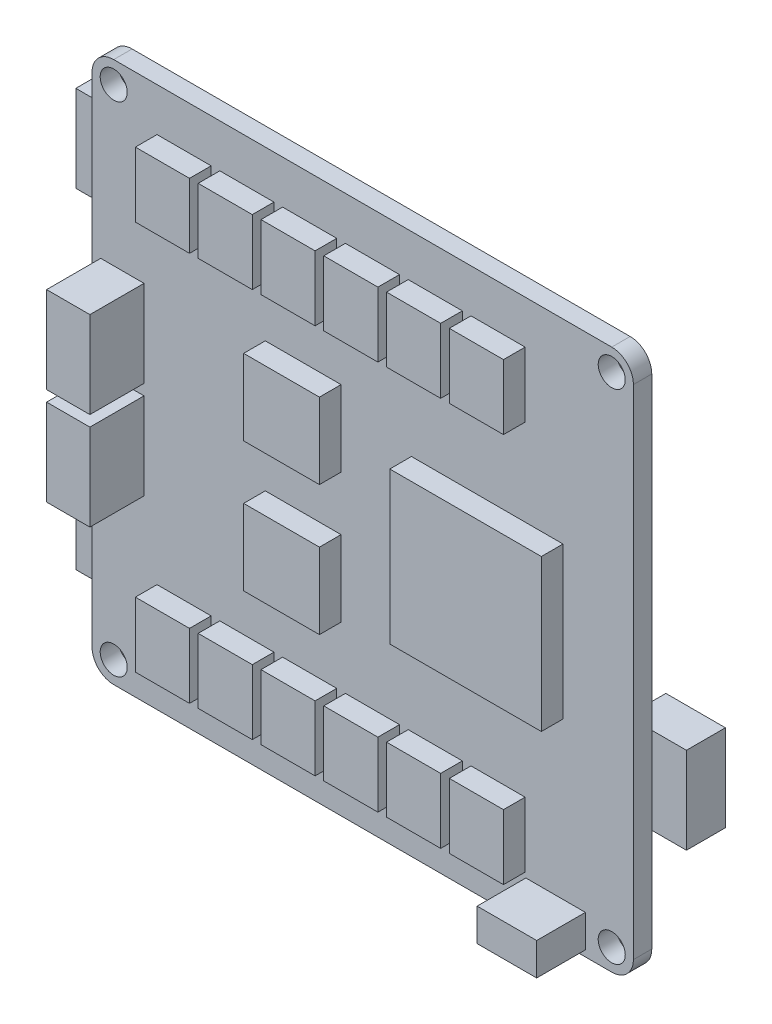
SolidWorks part; units mm, degrees
ref_plane "Ebene vorne" through (0, 0, 0) normal (0, 0, 1) x (1, 0, 0)
ref_plane "Ebene oben" through (0, 0, 0) normal (0, 1, 0) x (1, 0, 0)
ref_plane "Ebene rechts" through (0, 0, 0) normal (1, 0, 0) x (0, 0, -1)
sketch "Skizze1" plane through (0, 0, 0) normal (0, 0, 1) x (1, 0, 0)
  line L0 (0, 53.8417) -> (0, -53.7398) construction
  line L1 (-62.6849, 0) -> (55.7974, 0) construction
  line L2 (-25, -25) -> (-25, 25)
  line L3 (-25, 25) -> (25, 25)
  line L4 (25, -25) -> (25, 25)
  line L5 (-25, -25) -> (25, -25)
  circle A0 centre (-23, 23) radius 1.25
  circle A1 centre (23, 23) radius 1.25
  circle A2 centre (23, -23) radius 1.25
  circle A3 centre (-23, -23) radius 1.25
  point P9 (0, 25)
  point P10 (0, -25)
  point P12 (25, 0)
  point P13 (-25, 0)
  dimension "D3" = 2.5
  dimension "D1" = 50
  dimension "D2" = 50
  dimension "D4" = 46
  dimension "D5" = 46
extrude "Aufsatz-Linear austragen1" add sketch "Skizze1" along normal blind 1.7
fillet "Verrundung1" radius 2 4 edges at (-25, -25, 0.85) (25, -25, 0.85) (25, 25, 0.85) (-25, 25, 0.85)
sketch "Skizze2" plane through (0, 0, 1.7) normal (0, 0, 1) x (1, 0, 0)
  line L0 (-35.7245, 0) -> (33.2433, 0) construction
  line L1 (4.5, 7) -> (18.5, 7)
  line L2 (4.5, 7) -> (4.5, -7)
  line L3 (4.5, -7) -> (18.5, -7)
  line L4 (18.5, 7) -> (18.5, -7)
  line L5 (-9, 9.5) -> (-2, 9.5)
  line L6 (-9, 9.5) -> (-9, 2.5)
  line L7 (-9, 2.5) -> (-2, 2.5)
  line L8 (-2, 9.5) -> (-2, 2.5)
  line L9 (-2, -9.5) -> (-2, -2.5)
  line L10 (-9, -2.5) -> (-2, -2.5)
  line L11 (-9, -9.5) -> (-9, -2.5)
  line L12 (-9, -9.5) -> (-2, -9.5)
  line L13 (-13.2, 21) -> (-8.2, 21)
  line L14 (-19, 21) -> (-14, 21)
  line L15 (-19, 21) -> (-19, 15)
  line L16 (-19, 15) -> (-14, 15)
  line L17 (-14, 21) -> (-14, 15)
  line L18 (-13.2, 21) -> (-13.2, 15)
  line L19 (-13.2, 15) -> (-8.2, 15)
  line L20 (-8.2, 21) -> (-8.2, 15)
  line L21 (-7.4, 21) -> (-2.4, 21)
  line L22 (-7.4, 21) -> (-7.4, 15)
  line L23 (-7.4, 15) -> (-2.4, 15)
  line L24 (-2.4, 21) -> (-2.4, 15)
  line L25 (-1.6, 21) -> (3.4, 21)
  line L26 (-1.6, 21) -> (-1.6, 15)
  line L27 (-1.6, 15) -> (3.4, 15)
  line L28 (3.4, 21) -> (3.4, 15)
  line L29 (4.2, 21) -> (9.2, 21)
  line L30 (4.2, 21) -> (4.2, 15)
  line L31 (4.2, 15) -> (9.2, 15)
  line L32 (9.2, 21) -> (9.2, 15)
  line L33 (10, 21) -> (15, 21)
  line L34 (10, 21) -> (10, 15)
  line L35 (10, 15) -> (15, 15)
  line L36 (15, 21) -> (15, 15)
  line L37 (15, -21) -> (15, -15)
  line L38 (10, -15) -> (15, -15)
  line L39 (10, -21) -> (10, -15)
  line L40 (10, -21) -> (15, -21)
  line L41 (9.2, -21) -> (9.2, -15)
  line L42 (4.2, -15) -> (9.2, -15)
  line L43 (4.2, -21) -> (4.2, -15)
  line L44 (4.2, -21) -> (9.2, -21)
  line L45 (3.4, -21) -> (3.4, -15)
  line L46 (-1.6, -15) -> (3.4, -15)
  line L47 (-1.6, -21) -> (-1.6, -15)
  line L48 (-1.6, -21) -> (3.4, -21)
  line L49 (-2.4, -21) -> (-2.4, -15)
  line L50 (-7.4, -15) -> (-2.4, -15)
  line L51 (-7.4, -21) -> (-7.4, -15)
  line L52 (-7.4, -21) -> (-2.4, -21)
  line L53 (-8.2, -21) -> (-8.2, -15)
  line L54 (-13.2, -15) -> (-8.2, -15)
  line L55 (-13.2, -21) -> (-13.2, -15)
  line L56 (-14, -21) -> (-14, -15)
  line L57 (-19, -15) -> (-14, -15)
  line L58 (-19, -21) -> (-19, -15)
  line L59 (-19, -21) -> (-14, -21)
  line L60 (-13.2, -21) -> (-8.2, -21)
  line L61 (25, -23) -> (25, 23) construction
  line L62 (-25, 23) -> (-25, -23) construction
  line L63 (23, 25) -> (-23, 25) construction
  dimension "D1" = 14
  dimension "D2" = 14
  dimension "D3" = 7
  dimension "D4" = 7
  dimension "D5" = 5
  dimension "D6" = 6
  dimension "D8" = 6.5
  dimension "D9" = 34
  dimension "D10" = 6
  dimension "D11" = 4
  dimension "D12" = 19
  dimension "D13" = 16
  dimension "D7" = 6
extrude "Aufsatz-Linear austragen2" add sketch "Skizze2" along normal blind 2
sketch "Skizze3" plane through (0, 0, 1.7) normal (0, 0, 1) x (1, 0, 0)
  line L0 (-37.4139, 0) -> (32.6051, 0) construction
  line L1 (-20.2, -8.5) -> (-20.2, -0.5)
  line L2 (-24.2, 8.5) -> (-20.2, 8.5)
  line L3 (-24.2, 8.5) -> (-24.2, 0.5)
  line L4 (-24.2, 0.5) -> (-20.2, 0.5)
  line L5 (-20.2, 8.5) -> (-20.2, 0.5)
  line L6 (-24.2, -0.5) -> (-20.2, -0.5)
  line L7 (-24.2, -8.5) -> (-24.2, -0.5)
  line L8 (-24.2, -8.5) -> (-20.2, -8.5)
  line L9 (-25, 23) -> (-25, -23) construction
  dimension "D1" = 4
  dimension "D2" = 8
  dimension "D3" = 0.8
  dimension "D4" = 17
extrude "Aufsatz-Linear austragen3" add sketch "Skizze3" along normal blind 5
sketch "Skizze5" plane through (0, 0, 1.7) normal (0, 0, 1) x (1, 0, 0)
  line L1 (15.0672, -21.4338) -> (20.5672, -21.4338)
  line L2 (15.0672, -21.4338) -> (15.0672, -24.4338)
  line L3 (15.0672, -24.4338) -> (20.5672, -24.4338)
  line L4 (20.5672, -21.4338) -> (20.5672, -24.4338)
  dimension "D1" = 5.5
  dimension "D2" = 3
extrude "Aufsatz-Linear austragen5" add sketch "Skizze5" along normal blind 4.5
sketch "Skizze6" plane through (0, 0, 0) normal (0, 0, -1) x (-1, 0, 0)
  line L0 (-39.4997, 0) -> (35.3277, 0) construction
  line L1 (0, 28.1275) -> (0, -28.1275) construction
  line L2 (22.7, 19.25) -> (22.7, 11.25)
  line L3 (22.7, 11.25) -> (28.2, 11.25)
  line L4 (28.2, 11.25) -> (28.2, 19.25)
  line L5 (28.2, 19.25) -> (22.7, 19.25)
  line L6 (28.2, -19.25) -> (22.7, -19.25)
  line L7 (28.2, -11.25) -> (28.2, -19.25)
  line L8 (22.7, -11.25) -> (28.2, -11.25)
  line L9 (22.7, -19.25) -> (22.7, -11.25)
  line L10 (23, -25) -> (-23, -25) construction
  line L11 (-28.2, -5.5) -> (-22.7, -5.5)
  line L12 (-28.2, -5.5) -> (-28.2, -13.5)
  line L13 (-28.2, -13.5) -> (-22.7, -13.5)
  line L14 (-22.7, -5.5) -> (-22.7, -13.5)
  line L15 (25, 23) -> (25, -23) construction
  line L16 (-25, -23) -> (-25, 23) construction
  dimension "D1" = 8
  dimension "D2" = 5.5
  dimension "D3" = 38.5
  dimension "D4" = 11.5
  dimension "D5" = 3.2
  dimension "D6" = 3.2
extrude "Aufsatz-Linear austragen6" add sketch "Skizze6" along normal blind 3.6
